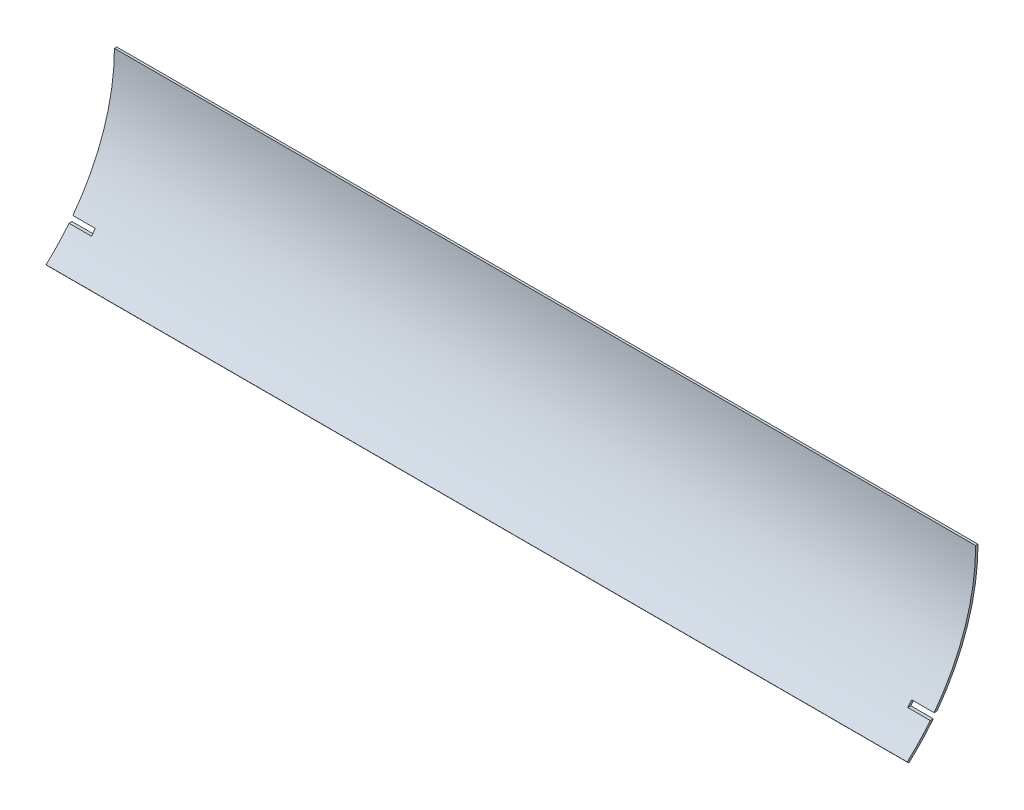
SolidWorks part; units mm, degrees
ref_plane "Front Plane" through (0, 0, 0) normal (0, 0, 1) x (1, 0, 0)
ref_plane "Top Plane" through (0, 0, 0) normal (0, 1, 0) x (1, 0, 0)
ref_plane "Right Plane" through (0, 0, 0) normal (1, 0, 0) x (0, 0, -1)
sketch "Sketch2" plane through (0, 0, 0) normal (1, 0, 0) x (0, 0, -1)
  arc A1 (93.6625, -104.5048) -> (140.335, 0) centre (0, 0) ccw
  dimension "D1" = 140.335
extrude "Extrude-Thin1" add sketch "Sketch2" along normal blind 584.2 thin thin type mid plane wall 1.5875
sketch "Sketch3" plane through (0, 0, 0) normal (0, 0, 1) x (1, 0, 0)
  line L0 (0, -87.4037) -> (15.24, -87.4037)
  line L1 (0, 0) -> (0, -103.9137) construction
  line L2 (15.24, -87.4037) -> (15.24, -84.1017)
  line L3 (15.24, -84.1017) -> (0, -84.1017)
  line L4 (0, -84.1017) -> (0, -87.4037)
  line L5 (292.1, -103.9137) -> (292.1, 36.2793) construction
  line L6 (584.2, -103.9137) -> (0, -103.9137) construction
  line L7 (584.2, -84.1017) -> (584.2, -87.4037)
  line L8 (568.96, -84.1017) -> (584.2, -84.1017)
  line L9 (568.96, -87.4037) -> (568.96, -84.1017)
  line L10 (584.2, -87.4037) -> (568.96, -87.4037)
  dimension "D1" = 3.302
  dimension "D2" = 15.24
  dimension "D3" = 16.51
extrude "Cut-Extrude1" cut sketch "Sketch3" against normal through all
